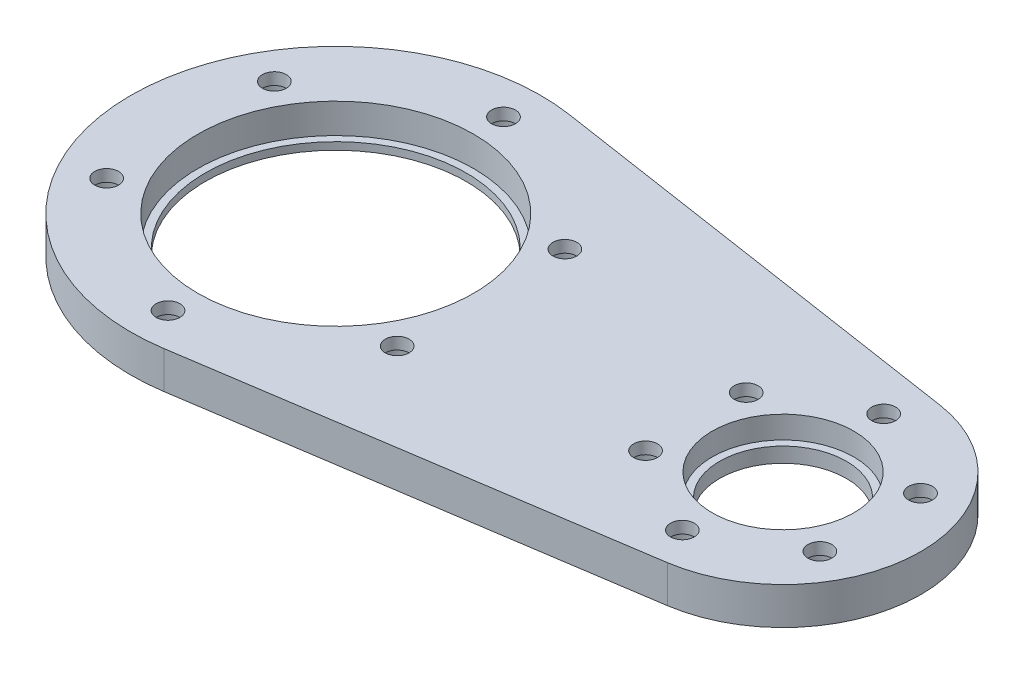
SolidWorks part; units mm, degrees
other "마크업1"
sketch "스케치8" plane through (80, 10, 22.5) normal (0.0741, 0.9433, 0.3234) x (0.9972, -0.0727, -0.0163)
sketch "스케치15" plane through (100, 13, 22.5) normal (0.0741, 0.9433, 0.3234) x (0.9972, -0.0727, -0.0163)
sketch "스케치16" plane through (100, 13, 22.5) normal (0.0741, 0.9433, 0.3234) x (0.9972, -0.0727, -0.0163)
sketch "스케치17" plane through (75, 13, 22.5) normal (0.0741, 0.9433, 0.3234) x (0.9972, -0.0727, -0.0163)
sketch "스케치23" plane through (75, 13, 22.5) normal (0.0741, 0.9433, 0.3234) x (0.9972, -0.0727, -0.0163)
sketch "스케치24" plane through (75, 10, 22.5) normal (0.0741, 0.9433, 0.3234) x (0.9972, -0.0727, -0.0163)
sketch "스케치25" plane through (75, 10, 25) normal (0.0741, 0.9433, 0.3234) x (0.9972, -0.0727, -0.0163)
sketch "스케치27" plane through (75, 5, 25) normal (0.0741, 0.9433, 0.3234) x (0.9972, -0.0727, -0.0163)
sketch "스케치29" plane through (75, 5, 25) normal (0.0741, 0.9433, 0.3234) x (0.9972, -0.0727, -0.0163)
sketch "스케치30" plane through (75, 4, 25) normal (0.0741, 0.9433, 0.3234) x (0.9972, -0.0727, -0.0163)
material "7075-T6 (SN)"
ref_plane "정면" through (0, 0, 0) normal (0, 0, 1) x (1, 0, 0)
ref_plane "윗면" through (0, 0, 0) normal (0, 1, 0) x (1, 0, 0)
ref_plane "우측면" through (0, 0, 0) normal (1, 0, 0) x (0, 0, -1)
sketch "스케치1" plane through (0, 0, 0) normal (0, 1, 0) x (1, 0, 0)
  circle A0 centre (0, 0) radius 17.5
  circle A1 centre (0, 0) radius 27.5
  dimension "D1" = 35
  dimension "D2" = 55
extrude "보스-돌출1" add sketch "스케치1" along normal blind 4 contours A1 | A0
sketch "스케치2" plane through (0, 4, 0) normal (0, 1, 0) x (1, 0, 0)
  circle A0 centre (0, 0) radius 18.5
  circle A1 centre (0, 0) radius 27.5 construction
  circle A2 centre (0, 0) radius 27.5
  dimension "D1" = 37
extrude "보스-돌출2" add sketch "스케치2" along normal blind 5
sketch "스케치3" plane through (0, 9, 0) normal (0, 1, 0) x (1, 0, 0)
  line L0 (4.125, 27.1889) -> (62.775, 18.2907)
  line L1 (0, 0) -> (60, 0) construction
  line L2 (4.125, -27.1889) -> (62.775, -18.2907)
  circle A0 centre (0, 0) radius 27.5 construction
  arc A1 (4.125, -27.1889) -> (4.125, 27.1889) centre (0, 0) ccw
  arc A2 (62.775, -18.2907) -> (62.775, 18.2907) centre (60, 0) ccw
  dimension "D2" = 37
  dimension "D1" = 60
extrude "보스-돌출3" add sketch "스케치3" against normal blind 9
sketch "스케치7" plane through (0, 4, 0) normal (0, 1, 0) x (1, 0, 0)
  circle A0 centre (0, 0) radius 18.5 construction
  circle A1 centre (0, 0) radius 18.5
extrude "컷-돌출4" cut sketch "스케치7" against normal blind 3
sketch "스케치13" plane through (0, 0, 0) normal (0, -1, 0) x (1, 0, 0)
  circle A0 centre (60, 0) radius 9.5
  dimension "D1" = 19
extrude "컷-돌출9" cut sketch "스케치13" against normal blind 7
sketch "스케치14" plane through (0, 7, 0) normal (0, -1, 0) x (1, 0, 0)
  circle A0 centre (60, 0) radius 8.5
  dimension "D1" = 17
extrude "컷-돌출10" cut sketch "스케치14" against normal through all
sketch "스케치26" plane through (0, 0, 0) normal (1, 0, 0) x (0, 0, -1)
  line L0 (18.2907, 9) -> (-18.2907, 9) construction
  line L1 (-33.8225, 18.2258) -> (31.4643, 18.2258)
  line L2 (-33.8225, 18.2258) -> (-33.8225, 5)
  line L3 (-33.8225, 5) -> (31.4643, 5)
  line L4 (31.4643, 18.2258) -> (31.4643, 5)
  dimension "D1" = 4
extrude "컷-돌출11" cut sketch "스케치26" against normal mid plane 2222
sketch "스케치28" plane through (0, 0, 0) normal (0, -1, 0) x (1, 0, 0)
  circle A0 centre (60, 0) radius 8.5
  circle A1 centre (60, 0) radius 9.5
  circle A2 centre (60, 0) radius 9.5 construction
  dimension "D1" = 17
extrude "보스-돌출4" add sketch "스케치28" against normal blind 2
sketch "스케치31" plane through (0, 0, 0) normal (0, -1, 0) x (1, 0, 0)
  circle A0 centre (0, 0) radius 22.5 construction
  circle A1 centre (0, 0) radius 17.5 construction
  point P2 (36.2446, 31.0278)
  dimension "D1" = 45
hole_wizard "M3 육각 소켓 머리 캡 나사용 카운터보어1" positions "스케치32" profile "스케치33" counterbore size "M3" standard "ISO" end condition through all
sketch "스케치32" plane through (0, 0, 0) normal (0, -1, 0) x (-1, 0, 0)
  circle A0 centre (0, 0) radius 22.5 construction
  point P0 (0, 22.5)
sketch "스케치33" plane through (0, 0, -22.5) normal (1, 0, 0) x (0, 0, -1)
  line L0 (0, 0) -> (0, 5)
  line L1 (0, 5) -> (1.6, 5)
  line L3 (1.6, 5) -> (1.6, 3.4)
  line L4 (1.6, 3.4) -> (3.25, 3.4)
  line L5 (3.25, 3.4) -> (3.25, 0)
  line L7 (3.25, 0) -> (0, 0)
  line L11 (0, -6.35) -> (0, 107.95) construction
  dimension "관통 구멍 지름" = 3.2
  dimension "관통 구멍 깊이" = 5
  dimension "카운터보어 지름" = 6.5
  dimension "카운터보어 깊이" = 3.4
pattern_circular "원형 패턴1" count 6 over 360 about axis through (0, 0, 0) along (0, 1, 0) of "M3 육각 소켓 머리 캡 나사용 카운터보어1"
sketch "스케치34" plane through (0, 0, 0) normal (0, -1, 0) x (1, 0, 0)
  circle A0 centre (60, 0) radius 13.5 construction
  circle A1 centre (60, 0) radius 8.5 construction
  dimension "D1" = 27
hole_wizard "M3 육각 소켓 머리 캡 나사용 카운터보어2" positions "스케치35" profile "스케치36" counterbore size "M3" standard "ISO" end condition through all
sketch "스케치35" plane through (0, 0, 0) normal (0, -1, 0) x (-1, 0, 0)
  circle A0 centre (-60, 0) radius 13.5 construction
  point P0 (-60, 13.5)
sketch "스케치36" plane through (60, 0, -13.5) normal (1, 0, 0) x (0, 0, -1)
  line L0 (0, 0) -> (0, 5)
  line L1 (0, 5) -> (1.6, 5)
  line L3 (1.6, 5) -> (1.6, 3.4)
  line L4 (1.6, 3.4) -> (3.25, 3.4)
  line L5 (3.25, 3.4) -> (3.25, 0)
  line L7 (3.25, 0) -> (0, 0)
  line L11 (0, -6.35) -> (0, 107.95) construction
  dimension "관통 구멍 지름" = 3.2
  dimension "관통 구멍 깊이" = 5
  dimension "카운터보어 지름" = 6.5
  dimension "카운터보어 깊이" = 3.4
pattern_circular "원형 패턴2" count 6 over 360 about axis through (60, 0, 0) along (0, 1, 0) of "M3 육각 소켓 머리 캡 나사용 카운터보어2"
